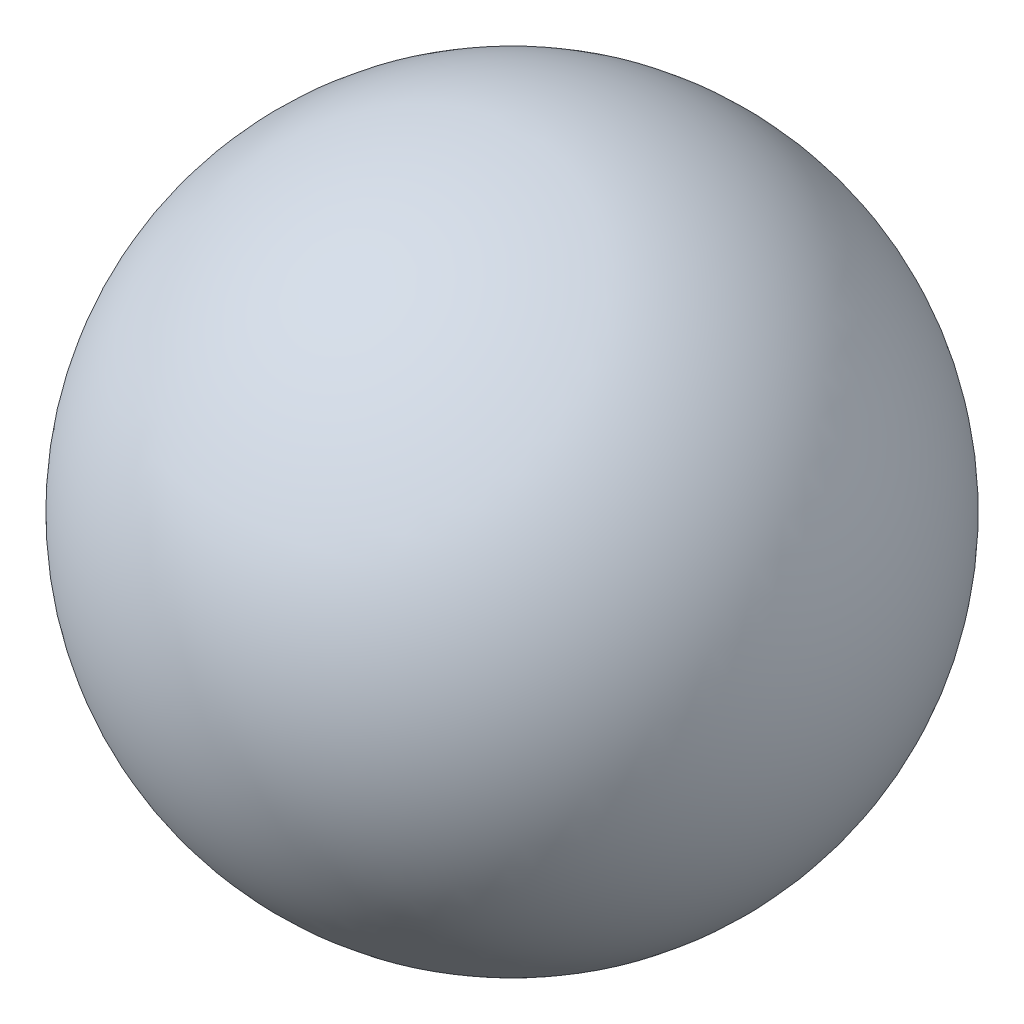
SolidWorks part; units mm, degrees
ref_plane "前视基准面" through (0, 0, 0) normal (0, 0, 1) x (1, 0, 0)
ref_plane "上视基准面" through (0, 0, 0) normal (0, 1, 0) x (1, 0, 0)
ref_plane "右视基准面" through (0, 0, 0) normal (1, 0, 0) x (0, 0, -1)
sketch "草图1" plane through (0, 0, 0) normal (0, 0, 1) x (1, 0, 0)
  line L0 (0, 2.5) -> (0, -2.5)
  arc A0 (0, -2.5) -> (0, 2.5) centre (0, 0) ccw
  dimension "D1" = 5
revolve "旋转1" add sketch "草图1" angle 360 about L0
sketch "草图2" plane through (0, 0, 0) normal (0, 0, 1) x (1, 0, 0)
  line L0 (0, 0) -> (0, 3.1184) construction
  line L1 (0, 0) -> (-4.067, 0) construction
sketch "草图3" plane through (0, 0, 0) normal (0, 1, 0) x (1, 0, 0)
  line L0 (0, 0) -> (0, 3.7288) construction
